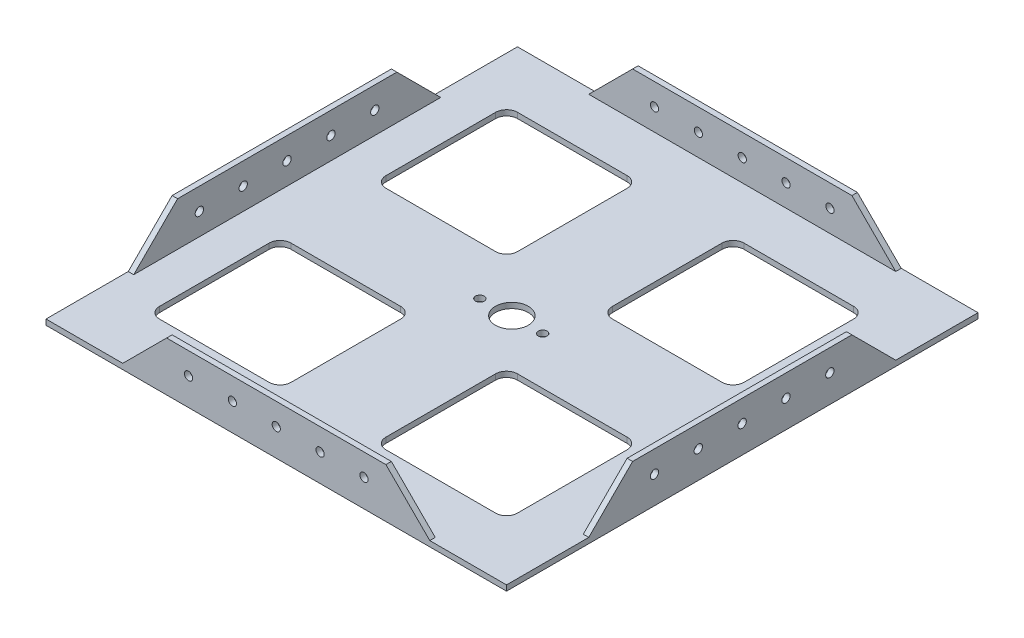
SolidWorks part; units mm, degrees
ref_plane "Front Plane" through (0, 0, 0) normal (0, 0, 1) x (1, 0, 0)
ref_plane "Top Plane" through (0, 0, 0) normal (0, 1, 0) x (1, 0, 0)
ref_plane "Right Plane" through (0, 0, 0) normal (1, 0, 0) x (0, 0, -1)
sketch "Sketch2" plane through (0, 0, 0) normal (0, 1, 0) x (1, 0, 0)
  line L1 (0, 0) -> (266.7, 0)
  line L2 (0, 0) -> (0, 273.05)
  line L3 (0, 273.05) -> (266.7, 273.05)
  line L4 (266.7, 0) -> (266.7, 273.05)
  dimension "D1" = 266.7
  dimension "D2" = 273.05
extrude "Boss-Extrude1" add sketch "Sketch2" along normal blind 3.175
sketch "Sketch3" plane through (0, 3.175, 0) normal (0, 1, 0) x (1, 0, 0)
  line L0 (133.35, 273.05) -> (133.35, 0) construction
  line L3 (266.7, 273.05) -> (0, 273.05) construction
  line L4 (0, 0) -> (266.7, 0) construction
  circle A0 centre (133.2625, 136.525) radius 9.525
  dimension "D1" = 19.05
extrude "Cut-Extrude1" cut sketch "Sketch3" against normal through all
sketch "Sketch4" plane through (0, 3.175, 0) normal (0, 1, 0) x (1, 0, 0)
  line L1 (26.5237, 240.2105) -> (102.7237, 240.2105)
  line L2 (26.5237, 240.2105) -> (26.5237, 164.0105)
  line L3 (26.5237, 164.0105) -> (102.7237, 164.0105)
  line L4 (102.7237, 240.2105) -> (102.7237, 164.0105)
  line L5 (157.6605, 240.2105) -> (233.8605, 240.2105)
  line L6 (157.6605, 240.2105) -> (157.6605, 164.0105)
  line L7 (157.6605, 164.0105) -> (233.8605, 164.0105)
  line L8 (233.8605, 240.2105) -> (233.8605, 164.0105)
  line L9 (26.5237, 109.0395) -> (102.7237, 109.0395)
  line L10 (26.5237, 109.0395) -> (26.5237, 32.8395)
  line L11 (26.5237, 32.8395) -> (102.7237, 32.8395)
  line L12 (102.7237, 109.0395) -> (102.7237, 32.8395)
  line L13 (157.6605, 109.0395) -> (233.8605, 109.0395)
  line L14 (157.6605, 109.0395) -> (157.6605, 32.8395)
  line L15 (157.6605, 32.8395) -> (233.8605, 32.8395)
  line L16 (233.8605, 109.0395) -> (233.8605, 32.8395)
  line L20 (266.7, 273.05) -> (0, 273.05) construction
  line L21 (0, 273.05) -> (0, 0) construction
  line L22 (0, 0) -> (266.7, 0) construction
  line L23 (266.7, 0) -> (266.7, 273.05) construction
  dimension "D2" = 32.8395
  dimension "D3" = 76.2
  dimension "D4" = 76.2
  dimension "D5" = 26.5237
  dimension "D6" = 26.5237
  dimension "D7" = 76.2
  dimension "D8" = 76.2
  dimension "D9" = 32.8395
  dimension "D10" = 32.8395
  dimension "D11" = 76.2
  dimension "D12" = 76.2
  dimension "D13" = 32.8395
  dimension "D14" = 32.8395
  dimension "D15" = 76.2
  dimension "D16" = 76.2
  dimension "D17" = 32.8395
extrude "Cut-Extrude2" cut sketch "Sketch4" against normal through all
fillet "Fillet2" radius 6.35 16 edges at (157.6605, 1.5875, -109.0395) (233.8605, 1.5875, -109.0395) (233.8605, 1.5875, -32.8395) (157.6605, 1.5875, -32.8395) (26.5237, 1.5875, -109.0395) (26.5237, 1.5875, -32.8395) (102.7237, 1.5875, -32.8395) (102.7237, 1.5875, -109.0395) (233.8605, 1.5875, -240.2105) (233.8605, 1.5875, -164.0105) (157.6605, 1.5875, -240.2105) (157.6605, 1.5875, -164.0105) (26.5237, 1.5875, -164.0105) (102.7237, 1.5875, -164.0105) (102.7237, 1.5875, -240.2105) (26.5237, 1.5875, -240.2105)
sketch "Sketch5" plane through (0, 3.175, 0) normal (0, 1, 0) x (1, 0, 0)
  line L0 (266.7, 273.05) -> (0, 273.05) construction
  line L1 (44.45, 273.05) -> (222.25, 273.05)
  line L2 (44.45, 273.05) -> (44.45, 269.875)
  line L3 (44.45, 269.875) -> (222.25, 269.875)
  line L4 (222.25, 273.05) -> (222.25, 269.875)
  line L8 (266.7, 0) -> (266.7, 273.05) construction
  line L11 (0, 0) -> (266.7, 0) construction
  line L12 (44.45, 0) -> (222.25, 0)
  line L13 (44.45, 0) -> (44.45, 3.175)
  line L14 (44.45, 3.175) -> (222.25, 3.175)
  line L15 (222.25, 0) -> (222.25, 3.175)
  line L16 (0, 273.05) -> (0, 0) construction
  line L17 (266.7, 225.425) -> (263.525, 225.425)
  line L18 (266.7, 225.425) -> (266.7, 47.625)
  line L19 (266.7, 47.625) -> (263.525, 47.625)
  line L20 (263.525, 225.425) -> (263.525, 47.625)
  line L21 (0, 225.425) -> (3.175, 225.425)
  line L22 (0, 225.425) -> (0, 47.625)
  line L23 (0, 47.625) -> (3.175, 47.625)
  line L24 (3.175, 225.425) -> (3.175, 47.625)
  dimension "D1" = 3.175
  dimension "D2" = 177.8
  dimension "D3" = 44.45
  dimension "D4" = 177.8
  dimension "D5" = 44.45
  dimension "D6" = 3.175
  dimension "D7" = 177.8
  dimension "D8" = 47.625
  dimension "D9" = 3.175
  dimension "D10" = 177.8
  dimension "D11" = 3.175
  dimension "D12" = 47.625
extrude "Boss-Extrude2" add sketch "Sketch5" along normal blind 25.4
sketch "Sketch6" plane through (266.7, 0, 0) normal (1, 0, 0) x (0, 0, -1)
  line L0 (47.625, 3.175) -> (73.025, 28.575)
  line L1 (47.625, 28.575) -> (225.425, 28.575) construction
  line L2 (225.425, 3.175) -> (200.025, 28.575)
  line L3 (47.625, 3.175) -> (225.425, 3.175) construction
  line L4 (47.625, 3.175) -> (47.625, 28.575)
  line L5 (47.625, 28.575) -> (73.025, 28.575)
  line L6 (200.025, 28.575) -> (225.425, 28.575)
  line L7 (225.425, 28.575) -> (225.425, 3.175)
  dimension "D1" = 45
extrude "Cut-Extrude3" cut sketch "Sketch6" against normal through all
sketch "Sketch7" plane through (0, 0, 0) normal (0, 0, 1) x (1, 0, 0)
  line L0 (44.45, 3.175) -> (222.25, 3.175) construction
  line L1 (44.45, 3.175) -> (69.85, 28.575)
  line L2 (44.45, 28.575) -> (222.25, 28.575) construction
  line L3 (222.25, 3.175) -> (196.85, 28.575)
  line L4 (44.45, 3.175) -> (44.45, 28.575)
  line L5 (44.45, 28.575) -> (69.85, 28.575)
  line L6 (196.85, 28.575) -> (222.25, 28.575)
  line L7 (222.25, 28.575) -> (222.25, 3.175)
  dimension "D1" = 45
extrude "Cut-Extrude4" cut sketch "Sketch7" against normal through all
sketch "Sketch8" plane through (0, 3.175, 0) normal (0, 1, 0) x (1, 0, 0)
  line L0 (133.2625, 198.6841) -> (133.2625, 69.1743) construction
  line L1 (164.0105, 164.0105) -> (227.5105, 164.0105) construction
  circle A0 centre (151.1187, 136.525) radius 2.54
  circle A1 centre (115.4063, 135.8515) radius 2.54
  dimension "D1" = 5.08
  dimension "D2" = 17.8562
  dimension "D4" = 27.4855
  dimension "D5" = 35.7188
  dimension "D6" = 5.08
  dimension "D3" = 17.8562
extrude "Cut-Extrude5" cut sketch "Sketch8" against normal through all
sketch "Sketch10" plane through (0, 0, 0) normal (0, 0, 1) x (1, 0, 0)
  line L0 (69.85, 28.575) -> (196.85, 28.575) construction
  line L1 (133.35, 28.575) -> (133.35, 0) construction
  line L2 (0, 0) -> (266.7, 0) construction
  circle A0 centre (133.35, 15.875) radius 2.3813
  circle A1 centre (158.75, 15.875) radius 2.3813
  circle A2 centre (107.95, 15.875) radius 2.3813
  circle A3 centre (82.55, 15.875) radius 2.3813
  circle A6 centre (184.15, 15.875) radius 2.3813
  dimension "D1" = 12.7
  dimension "D3" = 4.7625
  dimension "D8" = 4.7625
  dimension "D9" = 4.7625
  dimension "D12" = 4.7625
  dimension "D13" = 4.7625
  dimension "D4" = 25.4
  dimension "D5" = 25.4
  dimension "D10" = 25.4
  dimension "D11" = 25.4
extrude "Cut-Extrude6" cut sketch "Sketch10" against normal through all
sketch "Sketch11" plane through (266.7, 0, 0) normal (1, 0, 0) x (0, 0, -1)
  line L0 (73.025, 28.575) -> (200.025, 28.575) construction
  line L2 (0, 3.175) -> (0, 0) construction
  circle A0 centre (136.4488, 15.875) radius 2.413
  circle A1 centre (111.0488, 15.875) radius 2.413
  circle A2 centre (85.6488, 15.875) radius 2.413
  circle A4 centre (161.8488, 15.875) radius 2.413
  circle A5 centre (187.2488, 15.875) radius 2.413
  dimension "D2" = 4.826
  dimension "D6" = 25.4
  dimension "D8" = 4.826
  dimension "D9" = 4.826
  dimension "D10" = 4.826
  dimension "D11" = 4.826
  dimension "D3" = 12.7
  dimension "D4" = 25.4
  dimension "D5" = 25.4
  dimension "D7" = 25.4
  dimension "D12" = 136.4488
extrude "Cut-Extrude7" cut sketch "Sketch11" against normal through all
